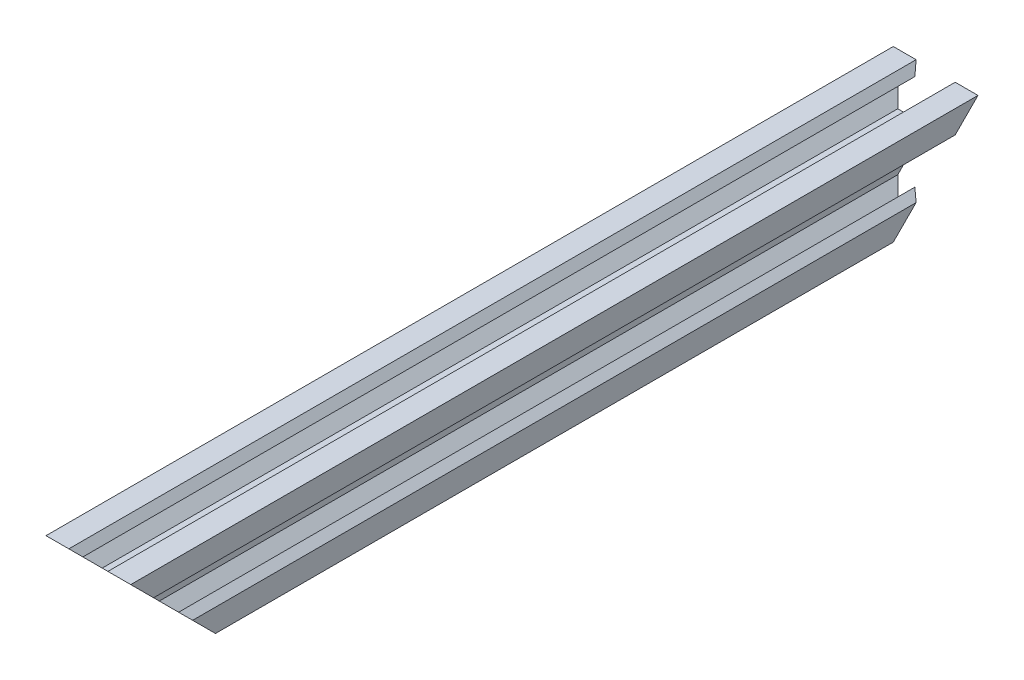
SolidWorks part; units mm, degrees
ref_plane "Front Plane" through (0, 0, 0) normal (0, 0, 1) x (1, 0, 0)
ref_plane "Top Plane" through (0, 0, 0) normal (0, 1, 0) x (1, 0, 0)
ref_plane "Right Plane" through (0, 0, 0) normal (1, 0, 0) x (0, 0, -1)
sketch "Sketch1" plane through (0, 0, 0) normal (0, 0, 1) x (1, 0, 0)
  line L0 (10, 10) -> (4.6104, 10) construction
  line L1 (10, 10) -> (10, 4.6104) construction
  line L2 (10, -10) -> (10, -4.6104) construction
  line L3 (10, -10) -> (4.6104, -10) construction
  line L4 (10, 10) -> (10, 4.6104)
  line L5 (6.5607, 5.5) -> (8.2, 5.5)
  line L6 (5.5, 8.2) -> (5.5, 6.5607)
  line L7 (10, 10) -> (4.6104, 10)
  line L8 (10, 10) -> (10, 4.6104)
  line L9 (6.5607, 5.5) -> (3.9, 2.8393)
  line L10 (5.5, 6.5607) -> (2.8393, 3.9)
  line L11 (10, 4.6104) -> (8.2, 3.1)
  line L12 (4.6104, 10) -> (3.1, 8.2)
  line L13 (8.2, 3.1) -> (8.2, 5.5)
  line L14 (3.1, 8.2) -> (5.5, 8.2)
  line L15 (-6.5607, 5.5) -> (-8.2, 5.5)
  line L16 (6.5607, -5.5) -> (8.2, -5.5)
  line L17 (3.1, -8.2) -> (5.5, -8.2)
  line L18 (8.2, -3.1) -> (8.2, -5.5)
  line L19 (4.6104, -10) -> (3.1, -8.2)
  line L20 (10, -4.6104) -> (8.2, -3.1)
  line L21 (0.5196, -3.9) -> (0, -3.6)
  line L22 (0.5196, 3.9) -> (0, 3.6)
  line L23 (3.6, 0) -> (3.9, -0.5196)
  line L24 (3.9, 0.5196) -> (3.6, 0)
  line L25 (3.9, 0.5196) -> (3.9, 2.8393)
  line L26 (2.8393, 3.9) -> (0.5196, 3.9)
  line L27 (3.9, -2.8393) -> (3.9, -0.5196)
  line L28 (2.8393, -3.9) -> (0.5196, -3.9)
  line L29 (5.5, -6.5607) -> (2.8393, -3.9)
  line L30 (6.5607, -5.5) -> (3.9, -2.8393)
  line L31 (10, -10) -> (10, -4.6104)
  line L32 (10, -10) -> (4.6104, -10)
  line L33 (5.5, -8.2) -> (5.5, -6.5607)
  line L34 (-6.5607, -5.5) -> (-8.2, -5.5)
  line L35 (10, -10) -> (10, -4.6104)
  line L36 (0, 0) -> (0, 8.2) construction
  line L37 (-10, -10) -> (-4.6104, -10) construction
  line L38 (-10, -10) -> (-10, -4.6104) construction
  line L39 (-10, 10) -> (-10, 4.6104) construction
  line L40 (-10, 10) -> (-4.6104, 10) construction
  line L41 (-10, -10) -> (-10, -4.6104)
  line L43 (-5.5, -8.2) -> (-5.5, -6.5607)
  line L44 (-10, -10) -> (-4.6104, -10)
  line L45 (-10, -10) -> (-10, -4.6104)
  line L46 (-6.5607, -5.5) -> (-3.9, -2.8393)
  line L47 (-5.5, -6.5607) -> (-2.8393, -3.9)
  line L48 (-2.8393, -3.9) -> (-0.5196, -3.9)
  line L49 (-3.9, -2.8393) -> (-3.9, -0.5196)
  line L50 (-2.8393, 3.9) -> (-0.5196, 3.9)
  line L51 (-3.9, 0.5196) -> (-3.9, 2.8393)
  line L52 (-3.9, 0.5196) -> (-3.6, 0)
  line L53 (-3.6, 0) -> (-3.9, -0.5196)
  line L54 (-0.5196, 3.9) -> (0, 3.6)
  line L55 (-0.5196, -3.9) -> (0, -3.6)
  line L56 (-10, -4.6104) -> (-8.2, -3.1)
  line L57 (-4.6104, -10) -> (-3.1, -8.2)
  line L58 (-8.2, -3.1) -> (-8.2, -5.5)
  line L59 (-3.1, -8.2) -> (-5.5, -8.2)
  line L60 (-10, -10) -> (10, -10) construction
  line L61 (-10, -10) -> (-10, 10) construction
  line L62 (-3.1, 8.2) -> (-5.5, 8.2)
  line L63 (-8.2, 3.1) -> (-8.2, 5.5)
  line L64 (-4.6104, 10) -> (-3.1, 8.2)
  line L65 (-10, 4.6104) -> (-8.2, 3.1)
  line L66 (-5.5, 6.5607) -> (-2.8393, 3.9)
  line L67 (-6.5607, 5.5) -> (-3.9, 2.8393)
  line L68 (-10, 10) -> (-10, 4.6104)
  line L69 (-10, 10) -> (-4.6104, 10)
  line L70 (-5.5, 8.2) -> (-5.5, 6.5607)
  line L71 (-10, 10) -> (10, 10) construction
  line L72 (-10, 10) -> (-10, 4.6104)
  line L73 (10, -10) -> (10, 10) construction
  line L74 (-10, -10) -> (10, 10) construction
  line L75 (-10, 10) -> (10, -10) construction
  circle A0 centre (0, 0) radius 2
  dimension "D7" = 4
  dimension "D1" = 20
  dimension "D2" = 5.3896
  dimension "D3" = 4.5
  dimension "D4" = 50
  dimension "D5" = 1.8
  dimension "D6" = 1.5104
  dimension "D8" = 5.5
  dimension "D9" = 120
  dimension "D10" = 0.3
  dimension "D11" = 2.3197
  dimension "D12" = 7.8
  dimension "D13" = 7.8
  dimension "D14" = 1.5
  dimension "D15" = 2.6607
extrude "Boss-Extrude1" add sketch "Sketch1" along normal mid plane 200 contours L70 L62 L64 L69 L68 L65 L63 L15 L67 L51 L52 L53 L49 L46 L34 L58 L56 L41 L44 L57 L59 L43 L47 L48 L55 L21 L28 L29 L33 L17 L19 L32 L31 L20 L18 L16 L30 L27 L23 L24 L25 L9 L5 L13 L11 L4 L7 L12 L14 L6 L10
sketch "Sketch2" plane through (10, 0, 0) normal (1, 0, 0) x (0, 0, -1)
  line L0 (100, 10) -> (80, -10)
  line L1 (-100, -10) -> (100, -10) construction
  line L2 (80, -10) -> (100, -10)
  line L3 (100, -10) -> (100, 10)
  line L4 (-100, 10) -> (-80, -10)
  line L5 (-80, -10) -> (-100, -10)
  line L6 (-100, -10) -> (-100, 10)
  dimension "D1" = 45
  dimension "D2" = 45
extrude "Cut-Extrude1" cut sketch "Sketch2" against normal up to next
